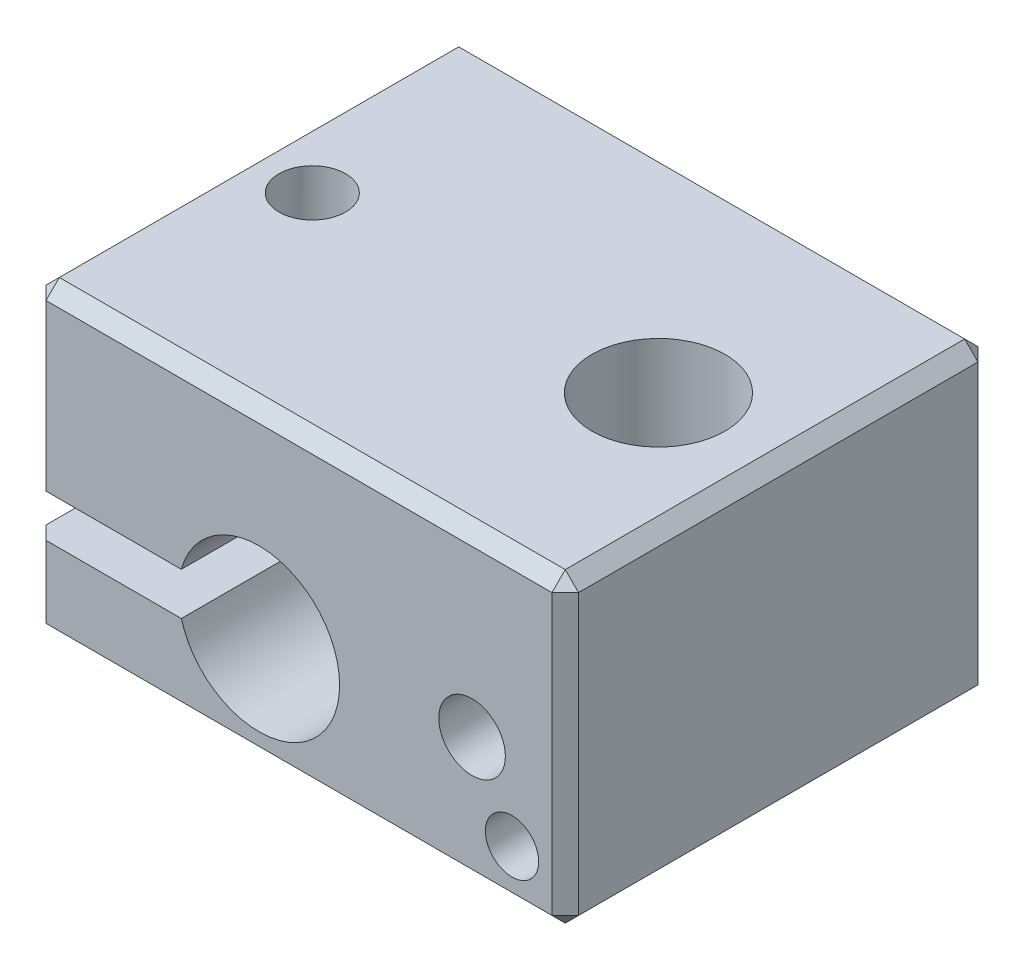
SolidWorks part; units mm, degrees
material "Liga 1345"
ref_plane "Plano frontal" through (0, 0, 0) normal (0, 0, 1) x (1, 0, 0)
ref_plane "Plano superior" through (0, 0, 0) normal (0, 1, 0) x (1, 0, 0)
ref_plane "Plano direito" through (0, 0, 0) normal (1, 0, 0) x (0, 0, -1)
sketch "Esboço1" plane through (0, 0, 0) normal (0, 0, 1) x (1, 0, 0)
  line L0 (-107.5953, -98.4118) -> (-87.5953, -98.4118) construction
  line L1 (-107.5803, -79.6503) -> (-101.9976, -79.6503)
  line L2 (-107.5803, -72.9503) -> (-87.5803, -72.9503)
  line L3 (-107.5803, -72.9503) -> (-107.5803, -79.6503)
  line L4 (-107.5803, -84.4503) -> (-87.5803, -84.4503)
  line L5 (-87.5803, -72.9503) -> (-87.5803, -84.4503)
  line L6 (-99.0803, -80.4503) -> (-110.4427, -80.4503) construction
  line L7 (-107.5803, -81.2503) -> (-101.9976, -81.2503)
  line L8 (-107.5803, -81.2503) -> (-107.5803, -84.4503)
  arc A0 (-101.9976, -81.2503) -> (-101.9976, -79.6503) centre (-99.0803, -80.4503) ccw
  point P8 (-91.0803, -79.6503)
  point P9 (-89.5803, -82.4503)
  dimension "D4" = 6.05
  dimension "D5" = 8.5
  dimension "D6" = 4
  dimension "D1" = 20
  dimension "D2" = 20
  dimension "D3" = 11.5
  dimension "D7" = 2
  dimension "D8" = 3.5
  dimension "D9" = 2
  dimension "D10" = 4.8
  dimension "D12" = 3.2
extrude "Ressalto-extrusão1" add sketch "Esboço1" along normal blind 16
hole_wizard "Broca de rosquear para tarraxa de M32" positions "Esboço3" profile "Esboço2" hole size "M3" standard "ISO"
sketch "Esboço3" plane through (0, 0, 16) normal (0, 0, 1) x (1, 0, 0)
  line L0 (-87.5803, -84.4503) -> (-87.5803, -72.9503) construction
  line L1 (-107.5803, -84.4503) -> (-87.5803, -84.4503) construction
  point P0 (-91.0803, -79.6503)
  dimension "D1" = 3.5
  dimension "D2" = 4.8
sketch "Esboço2" plane through (-91.0803, -79.6503, 16) normal (1, 0, 0) x (0, -1, 0)
  line L0 (0, 0) -> (0, 4.2511)
  line L1 (0, 4.2511) -> (1.25, 3.5)
  line L2 (1.25, 3.5) -> (1.25, 0)
  line L5 (1.25, 0) -> (0, 0)
  line L10 (0, 4.2511) -> (-1.25, 3.5) construction
  line L11 (0, -6.35) -> (0, 107.95) construction
  dimension "Hole Dia." = 2.5
  dimension "Hole Depth" = 3.5
  dimension "Drill Angle" = 118
sketch "Esboço4" plane through (0, 0, 16) normal (0, 0, 1) x (1, 0, 0)
  line L0 (-87.5803, -84.4503) -> (-87.5803, -72.9503) construction
  line L1 (-107.5803, -84.4503) -> (-87.5803, -84.4503) construction
  circle A0 centre (-89.5803, -82.4503) radius 1
  dimension "D1" = 2
  dimension "D2" = 2
  dimension "D3" = 2
extrude "Corte-extrusão1" cut sketch "Esboço4" against normal blind 2
hole_wizard "Broca de rosquear para tarraxa de M31" positions "Esboço7" profile "Esboço8" hole size "M3" standard "ISO"
sketch "Esboço7" plane through (0, -72.9503, 0) normal (0, 1, 0) x (1, 0, 0)
  line L0 (-87.5803, -16) -> (-107.5803, -16) construction
  line L2 (-87.5803, -16) -> (-87.5803, 0) construction
  point P0 (-105.0803, -8)
  point P9 (-105.0803, -8)
  dimension "D1" = 8
  dimension "D2" = 17.5
sketch "Esboço8" plane through (-105.0803, -72.9503, 8) normal (1, 0, 0) x (0, 0, 1)
  line L0 (0, 0) -> (0, 11.5)
  line L1 (0, 11.5) -> (1.25, 11.5)
  line L2 (1.25, 11.5) -> (1.25, 0)
  line L5 (1.25, 0) -> (0, 0)
  line L11 (0, -6.35) -> (0, 107.95) construction
  dimension "Thru Hole Dia." = 2.5
  dimension "Thru Hole Depth" = 11.5
sketch "Esboço9" plane through (0, -72.9503, 0) normal (0, 1, 0) x (1, 0, 0)
  point P7 (-92.0803, -8)
hole_wizard "Broca de rosquear para tarraxa de M61" positions "Esboço11" profile "Esboço10" hole size "M6" standard "ISO"
sketch "Esboço11" plane through (0, -72.9503, 0) normal (0, 1, 0) x (1, 0, 0)
  point P0 (-92.0803, -8)
sketch "Esboço10" plane through (-92.0803, -72.9503, 8) normal (1, 0, 0) x (0, 0, 1)
  line L0 (0, 0) -> (0, 11.5)
  line L1 (0, 11.5) -> (2.5, 11.5)
  line L2 (2.5, 11.5) -> (2.5, 0)
  line L5 (2.5, 0) -> (0, 0)
  line L11 (0, -6.35) -> (0, 107.95) construction
  dimension "Thru Hole Dia." = 5
  dimension "Thru Hole Depth" = 11.5
cosmetic thread "Representação de rosca1" parameters "D2"=6
chamfer "Chanfro1" distance 0.5 angle 45 14 edges at (-107.5803, -82.8503, 16) (-107.5803, -76.3003, 16) (-107.5803, -84.4503, 8) (-107.5803, -82.8503, 0) (-107.5803, -76.3003, 0) (-97.5803, -84.4503, 0) (-97.5803, -84.4503, 16) (-97.5803, -72.9503, 0) (-97.5803, -72.9503, 16) (-87.5803, -78.7003, 0) (-87.5803, -78.7003, 16) (-87.5803, -84.4503, 8) (-87.5803, -72.9503, 8) (-107.5803, -72.9503, 8)
sketch "Esboço12" plane through (0, 0, 16) normal (0, 0, 1) x (1, 0, 0)
  circle A0 centre (-89.5803, -82.4503) radius 0.8
extrude "Corte-extrusão2" cut sketch "Esboço12" against normal blind 4.5
hole_wizard "Furo com folga de M33" positions "Esboço14" profile "Esboço13" hole size "M3" standard "ISO"
sketch "Esboço14" plane through (0, -84.4503, 0) normal (0, -1, 0) x (-1, 0, 0)
  point P0 (105.0803, -8)
sketch "Esboço13" plane through (-105.0803, -84.4503, 8) normal (1, 0, 0) x (0, 0, -1)
  line L0 (0, 0) -> (0, 3.2)
  line L1 (0, 3.2) -> (1.6, 3.2)
  line L2 (1.6, 3.2) -> (1.6, 0)
  line L5 (1.6, 0) -> (0, 0)
  line L11 (0, -6.35) -> (0, 107.95) construction
  dimension "Thru Hole Dia." = 3.2
  dimension "Thru Hole Depth" = 3.2
